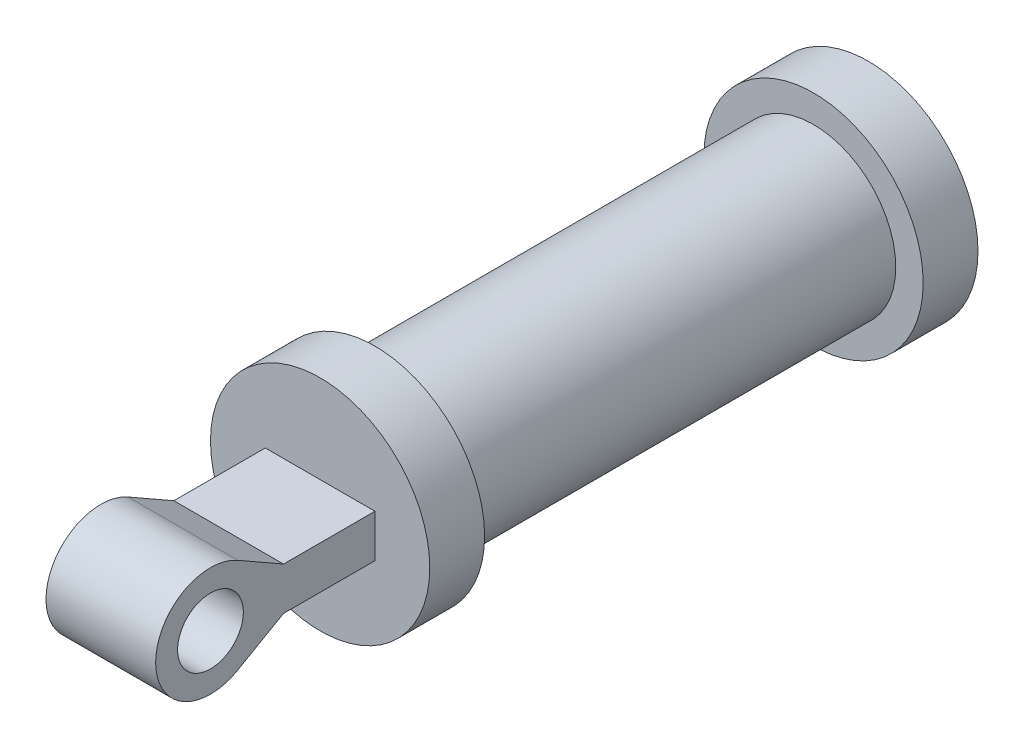
SolidWorks part; units mm, degrees
ref_plane "Front Plane" through (0, 0, 0) normal (0, 0, 1) x (1, 0, 0)
ref_plane "Top Plane" through (0, 0, 0) normal (0, 1, 0) x (1, 0, 0)
ref_plane "Right Plane" through (0, 0, 0) normal (1, 0, 0) x (0, 0, -1)
sketch "Sketch3" plane through (0, 0, 0) normal (0, 0, 1) x (1, 0, 0)
  circle A0 centre (0, 0) radius 10
extrude "Boss-Extrude3" add sketch "Sketch3" along normal blind 5
hole_wizard "CBORE for M4 Cheese Head Screw1" positions "Sketch15" profile "Sketch14" counterbore size "M4" standard "AS"
sketch "Sketch15" plane through (0, 0, 5) normal (0, 0, 1) x (1, 0, 0)
  point P0 (0, 0)
sketch "Sketch14" plane through (0, 0, 5) normal (1, 0, 0) x (0, -1, 0)
  line L0 (0, 0) -> (0, 8.9421)
  line L1 (0, 8.9421) -> (2.4, 7.5)
  line L2 (2.4, 7.5) -> (2.4, 2.6)
  line L3 (2.4, 2.6) -> (4, 2.6)
  line L5 (4, 2.6) -> (4, 0.025)
  line L6 (4, 0.025) -> (4.025, 0)
  line L7 (4.025, 0) -> (0, 0)
  line L8 (-4, 0.025) -> (-4.025, 0) construction
  line L10 (0, 8.9421) -> (-2.4, 7.5) construction
  line L11 (0, -6.35) -> (0, 107.95) construction
  dimension "Hole Dia." = 4.8
  dimension "Hole Depth" = 7.5
  dimension "C'Bore Dia." = 8
  dimension "C'Bore Depth" = 2.6
  dimension "Near C'Sink Dia." = 8.05
  dimension "Near C'Sink Angle" = 90
  dimension "Drill Angle" = 118
sketch "Sketch16" plane through (0, 0, 5) normal (0, 0, 1) x (1, 0, 0)
  circle A0 centre (0, 0) radius 7.5
extrude "Boss-Extrude7" add sketch "Sketch16" along normal blind 40
sketch "Sketch19" plane through (0, 0, 45) normal (0, 0, 1) x (1, 0, 0)
  circle A0 centre (0, 0) radius 4
extrude "Cut-Extrude3" cut sketch "Sketch19" against normal blind 40
sketch "Sketch20" plane through (0, 0, 45) normal (0, 0, 1) x (1, 0, 0)
  circle A0 centre (0, 0) radius 10
extrude "Boss-Extrude8" add sketch "Sketch20" along normal blind 5
sketch "Sketch21" plane through (0, 0, 50) normal (0, 0, 1) x (1, 0, 0)
  line L1 (-5.3768, -6.8498) -> (5.3768, -6.8498)
  line L2 (-5.3768, -6.8498) -> (-5.3768, 6.8498)
  line L3 (-5.3768, 6.8498) -> (5.3768, 6.8498)
  line L4 (5.3768, -6.8498) -> (5.3768, 6.8498)
  line L5 (-5.3768, -6.8498) -> (5.3768, 6.8498) construction
  line L6 (-5.3768, 6.8498) -> (5.3768, -6.8498) construction
  point P0 (0, 0)
  point P6 (-5.3768, 6.8498)
extrude "Boss-Extrude9" add sketch "Sketch21" along normal blind 20
sketch "Sketch24" plane through (5.3768, 0, 0) normal (1, 0, 0) x (0, 0, -1)
  line L0 (-70, -6.8498) -> (-70, 6.8498) construction
  line L1 (-50, 1.9522) -> (-58.3382, 1.9522)
  line L2 (-50, 10) -> (-50, -10) construction
  line L3 (-58.3382, 1.9522) -> (-62.5194, 4.3413)
  line L4 (-65, 0) -> (-35.1554, 0) construction
  line L5 (-58.3382, -1.9522) -> (-50, -1.9522)
  line L6 (-50, -1.9522) -> (-50.0777, 0)
  line L7 (-50.0777, 0) -> (-50, 1.9522)
  line L8 (-58.3382, -1.9522) -> (-62.5194, -4.3413)
  line L9 (-70, 6.8498) -> (-50, 6.8498)
  line L10 (-50, -6.8498) -> (-50, 6.8498) construction
  line L11 (-70, 6.8498) -> (-50, 6.8498) construction
  line L12 (-70, 6.8498) -> (-70, 0)
  line L13 (-70, 0) -> (-70, -6.8498)
  line L14 (-70, -6.8498) -> (-50, -6.8498)
  line L15 (-50, -6.8498) -> (-50, -1.9522)
  line L16 (-50, 6.8498) -> (-50, 1.9522)
  circle A0 centre (-65, 0) radius 5
  point P2 (-58.3382, -1.9522)
  line M5 (-50, -6.8498) -> (-50, 6.8498)
  line M6 (-50, 6.8498) -> (-70, 6.8498)
  line M7 (-70, 6.8498) -> (-70, -6.8498)
  line M8 (-70, -6.8498) -> (-50, -6.8498)
  dimension "D1" = 10
extrude "Cut-Extrude5" cut sketch "Sketch24" against normal through all contours A0 L3 L1 M5 M6 M7 | A0 L5 L8 M7 M8 M5
sketch "Sketch25" plane through (5.3768, 0, 0) normal (1, 0, 0) x (0, 0, -1)
  circle A0 centre (-65, 0) radius 3
extrude "Cut-Extrude6" cut sketch "Sketch25" against normal through all
sketch "Sketch27" plane through (0, 1.9522, 0) normal (0, 1, 0) x (1, 0, 0)
  line L0 (-5.3768, -50) -> (5.3768, -50) construction
  line L1 (-5, -71.0455) -> (5, -71.0455)
  line L2 (-5, -71.0455) -> (-5, -50)
  line L3 (-5, -50) -> (5, -50)
  line L4 (5, -71.0455) -> (5, -50)
  line L5 (-5, -71.0455) -> (5, -50) construction
  line L6 (-5, -50) -> (5, -71.0455) construction
  line L7 (-5, -50) -> (-8.1474, -50)
  line L8 (-8.1474, -50) -> (-8.1474, -71.0455)
  line L9 (-8.1474, -71.0455) -> (-5, -71.0455)
  line L10 (5, -71.0455) -> (7.6373, -71.0455)
  line L11 (7.6373, -71.0455) -> (7.6373, -50)
  line L12 (7.6373, -50) -> (5, -50)
  point P0 (0, -60.5228)
  line M8 (-5.3768, -50) -> (-5.3768, -58.3382)
  line M9 (-5.3768, -58.3382) -> (5.3768, -58.3382)
  line M10 (5.3768, -58.3382) -> (5.3768, -50)
  dimension "D1" = 10
extrude "Cut-Extrude7" cut sketch "Sketch27" against normal mid plane 20 contours L11 L12 L4 L10 M10 M9 | L8 L9 L2 L7 M9 M8
sketch "Sketch28" plane through (0, 0, 58.3382) normal (0, 0, 1) x (1, 0, 0)
  line L0 (-5.3768, -1.9522) -> (5.3768, -1.9522) construction
  line L1 (-5.3768, 1.9522) -> (-5, 1.9522)
  line L2 (-5.3768, 1.9522) -> (-5.3768, -1.9522)
  line L3 (-5.3768, -1.9522) -> (-5, -1.9522)
  line L4 (-5, 1.9522) -> (-5, -1.9522)
  line L5 (-5, 5) -> (-5, -5) construction
  line L7 (5.3768, 1.9522) -> (5, 1.9522)
  line L8 (5.3768, 1.9522) -> (5.3768, -1.9522)
  line L9 (5.3768, -1.9522) -> (5, -1.9522)
  line L10 (5, 1.9522) -> (5, -1.9522)
extrude "Cut-Extrude8" cut sketch "Sketch28" against normal up to surface (8.3382 mm away) up to face at (0, 0, 50)
scale "Scale1" scale about centroid uniform scaling yes scale factor 10
